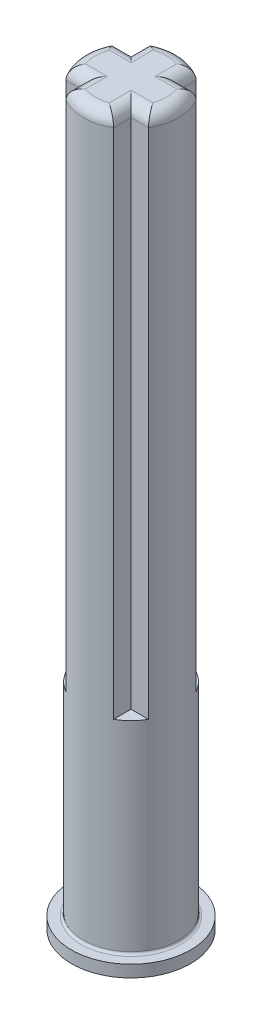
SolidWorks part; units mm, degrees
material "PBT General Purpose"
ref_plane "Front Plane" through (0, 0, 0) normal (0, 0, 1) x (1, 0, 0)
ref_plane "Top Plane" through (0, 0, 0) normal (0, 1, 0) x (1, 0, 0)
ref_plane "Right Plane" through (0, 0, 0) normal (1, 0, 0) x (0, 0, -1)
sketch "Sketch1" plane through (0, 0, 0) normal (0, 1, 0) x (1, 0, 0)
  line L1 (-1, -1.7321) -> (1, -1.7321)
  line L2 (-1, -1.7321) -> (-1, 1.7321)
  line L3 (-1, 1.7321) -> (1, 1.7321)
  line L4 (1, -1.7321) -> (1, 1.7321)
  line L5 (-1, -1.7321) -> (1, 1.7321) construction
  line L6 (-1, 1.7321) -> (1, -1.7321) construction
  line L7 (-1.7321, -1) -> (1.7321, -1)
  line L8 (-1.7321, -1) -> (-1.7321, 1)
  line L9 (-1.7321, 1) -> (1.7321, 1)
  line L10 (1.7321, -1) -> (1.7321, 1)
  line L11 (-1.7321, -1) -> (1.7321, 1) construction
  line L12 (-1.7321, 1) -> (1.7321, -1) construction
  arc A0 (-1.7321, 1) -> (-1.7321, -1) centre (0, 0) ccw
  arc A1 (-1, -1.7321) -> (1, -1.7321) centre (0, 0) ccw
  arc A2 (1.7321, -1) -> (1.7321, 1) centre (0, 0) ccw
  arc A3 (1, 1.7321) -> (-1, 1.7321) centre (0, 0) ccw
  dimension "D1" = 4
  dimension "D2" = 2
  dimension "D3" = 2
extrude "Boss-Extrude1" add sketch "Sketch1" along normal blind 22 contours L3 A3 | L2 L9 L4 L3 | L10 A2 | L7 L10 L9 L4 | L9 L2 L7 L4 | L9 L8 L7 L2 | L8 A0 | L7 L2 L1 L4 | L1 A1
sketch "Sketch2" plane through (0, 0, 0) normal (0, -1, 0) x (1, 0, 0)
  circle A0 centre (0, 0) radius 2
  dimension "D1" = 4
extrude "Boss-Extrude2" add sketch "Sketch2" along normal blind 9
sketch "Sketch3" plane through (0, -9, 0) normal (0, -1, 0) x (1, 0, 0)
  circle A0 centre (0, 0) radius 2.5
  dimension "D1" = 5
extrude "Boss-Extrude3" add sketch "Sketch3" against normal blind 0.5
fillet "Fillet1" radius 0.5 12 edges at (1, 22, -1.366) (1.366, 22, -1) (-2, 22, 0) (2, 22, 0) (1.366, 22, 1) (1, 22, 1.366) (0, 22, 2) (0, 22, -2) (-1, 22, 1.366) (-1.366, 22, 1) (-1.366, 22, -1) (-1, 22, -1.366)
fillet "Fillet2" radius 0.1 1 edges at (0, -8.5, -2)
